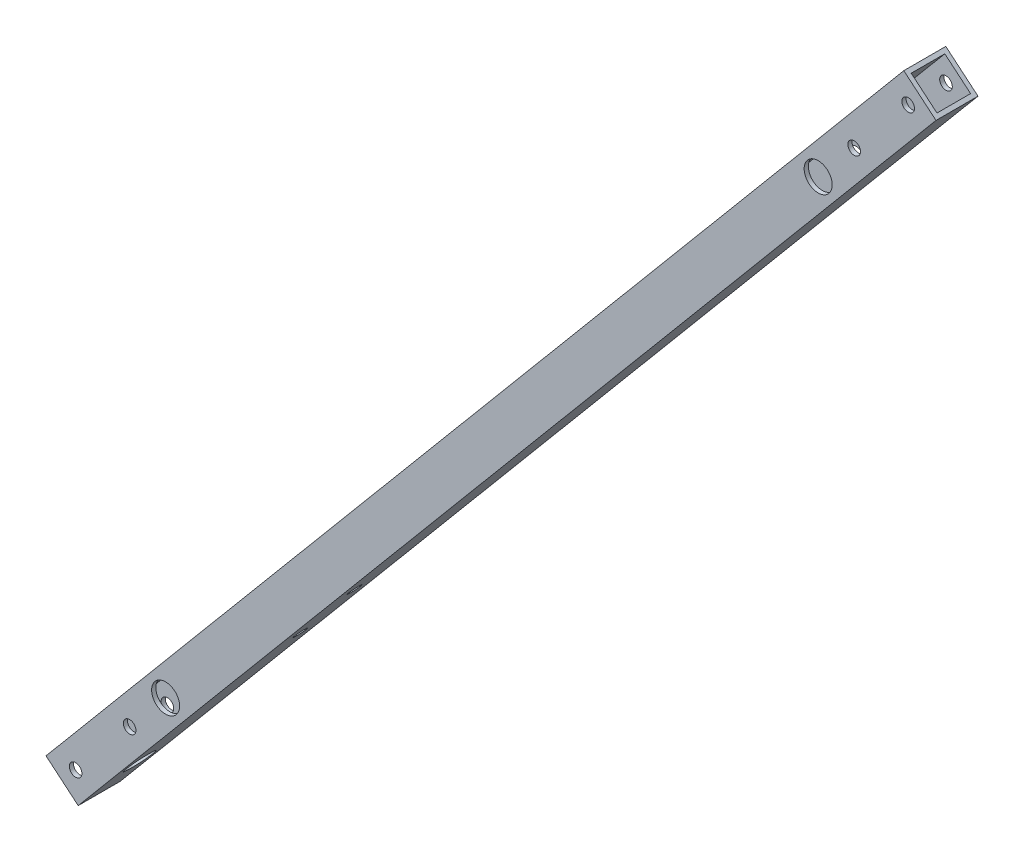
SolidWorks part; units mm, degrees
material "6063-T5"
ref_plane "正面" through (0, 0, 0) normal (0, 0, 1) x (1, 0, 0)
ref_plane "平面" through (0, 0, 0) normal (0, 1, 0) x (1, 0, 0)
ref_plane "右側面" through (0, 0, 0) normal (1, 0, 0) x (0, 0, -1)
sketch "ｽｹｯﾁ1" plane through (0, 0, 0) normal (0, 0, 1) x (1, 0, 0)
  line L0 (0, 0) -> (306.8848, 365.731) construction
  line L1 (306.8848, 365.731) -> (440, 0) construction
  line L2 (440, 0) -> (0, 0) construction
  line L3 (306.8848, 365.731) -> (306.8848, 0) construction
  line L4 (306.8848, 365.731) -> (0, 0)
  line L9 (306.8848, 365.731) -> (295.3941, 375.3729)
  line L11 (295.3941, 375.3729) -> (-11.4907, 9.6418)
  line L12 (-11.4907, 9.6418) -> (0, 0)
  dimension "D4" = 15
  dimension "D1" = 440
  dimension "D2" = 70
  dimension "D3" = 50
extrude "ﾎﾞｽ - 押し出し1" add sketch "ｽｹｯﾁ1" along normal blind 15
shell "ｼｪﾙ1" thickness 1.5
sketch "ｽｹｯﾁ3" plane through (0, 0, 15) normal (0, 0, 1) x (1, 0, 0)
  line L0 (306.8848, 365.731) -> (295.3941, 375.3729) construction
  line L1 (-5.7453, 4.8209) -> (301.1395, 370.552) construction
  line L2 (-11.4907, 9.6418) -> (0, 0) construction
  circle A3 centre (-0.9244, 10.5662) radius 2.25
  circle A4 centre (18.3592, 33.5476) radius 2.25
  circle A5 centre (277.0349, 341.8253) radius 2.25
  circle A6 centre (296.3185, 364.8066) radius 2.25
  circle A7 centre (31.215, 48.8685) radius 2.7
  circle A8 centre (264.1792, 326.5044) radius 2.7
  dimension "D1" = 4.5
  dimension "D2" = 5.4
  dimension "D3" = 7.5
  dimension "D4" = 30
  dimension "D5" = 4.5
  dimension "D6" = 4.5
  dimension "D7" = 7.5
  dimension "D8" = 30
  dimension "D9" = 20
  dimension "4" = 4.5
  dimension "D10" = 5.4
  dimension "D11" = 20
extrude "ｶｯﾄ - 押し出し1" cut sketch "ｽｹｯﾁ3" against normal blind 25
sketch "ｽｹｯﾁ6" plane through (0, 0, 15) normal (0, 0, 1) x (1, 0, 0)
  line L0 (306.8848, 365.731) -> (440, 0) construction
  line L1 (440, 0) -> (0, 0) construction
  line L2 (306.8848, 365.731) -> (0, 0) construction
  line L3 (97.6452, 116.369) -> (397.6452, 116.369) construction
  line L4 (97.6452, 116.369) -> (78.064, 116.369) construction
  line L5 (295.3941, 375.3729) -> (-11.4907, 9.6418) construction
  line L6 (78.064, 116.369) -> (74.8501, 112.5387) construction
  line L7 (74.8501, 112.5387) -> (86.3408, 102.8969) construction
  line L8 (86.3408, 102.8969) -> (97.6452, 116.369) construction
  line L10 (70.0292, 106.7934) -> (81.5199, 97.1516)
  line L11 (-11.4907, 9.6418) -> (0, 0) construction
  dimension "D1" = 440
  dimension "D2" = 300
  dimension "D3" = 5
  dimension "D4" = 126.8224
  dimension "D5" = 7.5
sketch "ｽｹｯﾁ5" plane through (-11.4907, 9.6418, 0) normal (-0.766, 0.6428, 0) x (0, 0, 1)
  line L0 (15, 477.428) -> (15, 0) construction
  line L1 (15, 0) -> (0, 0) construction
  circle A0 centre (7.5, 141.8224) radius 2.25
  circle A1 centre (7.5, 111.8224) radius 2.25
  circle A2 centre (7.5, 22.5) radius 2.7
  point P11 (7.5, 0)
  dimension "D2" = 7.5
  dimension "D3" = 30
  dimension "D4" = 15
  dimension "D5" = 4.5
  dimension "D6" = 4.5
  dimension "D8" = 22.5
  dimension "D7" = 5.4
  dimension "D1" = 7.5
extrude "ｶｯﾄ - 押し出し3" cut sketch "ｽｹｯﾁ5" against normal blind 20
sketch "ｽｹｯﾁ7" plane through (306.8848, 365.731, 0) normal (0.6428, 0.766, 0) x (0.766, -0.6428, 0)
  line L0 (-15, -15) -> (-15, 0) construction
  line L1 (-15, -15) -> (0, -15)
  line L2 (-15, -15) -> (-15, 0)
  line L3 (-15, 0) -> (0, 0)
  line L4 (0, -15) -> (0, 0)
  line L5 (-15, -15) -> (0, 0) construction
  line L6 (-15, 0) -> (0, -15) construction
  line L7 (-13.5, -13.5) -> (-1.5, -13.5)
  line L8 (-13.5, -13.5) -> (-13.5, -1.5)
  line L9 (-13.5, -1.5) -> (-1.5, -1.5)
  line L10 (-1.5, -13.5) -> (-1.5, -1.5)
  line L11 (-13.5, -13.5) -> (-1.5, -1.5) construction
  line L12 (-13.5, -1.5) -> (-1.5, -13.5) construction
  point P0 (-7.5, -7.5)
  point P6 (-7.5, -7.5)
extrude "ｶｯﾄ - 押し出し4" cut sketch "ｽｹｯﾁ7" against normal blind 1
hole_wizard "Ø10.0 (10) 直径の穴1" positions "ｽｹｯﾁ9" profile "ｽｹｯﾁ11" hole size "Ø10.0" standard "JIS"
sketch "ｽｹｯﾁ9" plane through (0, 0, 0) normal (0.766, -0.6428, 0) x (0, 0, -1)
  point P0 (-7.5, 22.5)
sketch "ｽｹｯﾁ11" plane through (14.4627, 17.236, 7.5) normal (0, 0, 1) x (0.6428, 0.766, 0)
  line L0 (0, 0) -> (0, 1.5)
  line L1 (0, 1.5) -> (5, 1.5)
  line L2 (5, 1.5) -> (5, 0)
  line L5 (5, 0) -> (0, 0)
  line L10 (0, 1.5) -> (-5, 1.5) construction
  line L11 (0, -6.35) -> (0, 107.95) construction
  dimension "穴の直径" = 10
  dimension "穴の深さ" = 1.5
  dimension "ﾄﾞﾘﾙ角度" = 180
hole_wizard "Ø10.0 (10) 直径の穴2" positions "ｽｹｯﾁ12" profile "ｽｹｯﾁ14" hole size "Ø10.0" standard "JIS"
sketch "ｽｹｯﾁ12" plane through (0, 0, 15) normal (0, 0, 1) x (1, 0, 0)
  point P0 (31.215, 48.8685)
  point P3 (264.1792, 326.5044)
sketch "ｽｹｯﾁ14" plane through (31.215, 48.8685, 15) normal (1, 0, 0) x (0, -1, 0)
  line L0 (0, 0) -> (0, 1.5)
  line L1 (0, 1.5) -> (5, 1.5)
  line L2 (5, 1.5) -> (5, 0)
  line L5 (5, 0) -> (0, 0)
  line L10 (0, 1.5) -> (-5, 1.5) construction
  line L11 (0, -6.35) -> (0, 107.95) construction
  dimension "穴の直径" = 10
  dimension "穴の深さ" = 1.5
  dimension "ﾄﾞﾘﾙ角度" = 180
